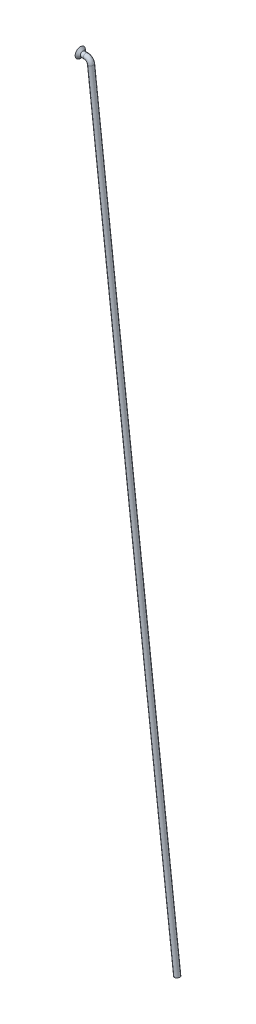
SolidWorks part; units mm, degrees
ref_plane "Plan de face" through (0, 0, 0) normal (0, 0, 1) x (1, 0, 0)
ref_plane "Plan de dessus" through (0, 0, 0) normal (0, 1, 0) x (1, 0, 0)
ref_plane "Plan de droite" through (0, 0, 0) normal (1, 0, 0) x (0, 0, -1)
sketch "Esquisse1" plane through (0, 0, 0) normal (0, 0, 1) x (1, 0, 0)
  line L1 (-1.7826, 0) -> (-4, 0)
  line L2 (0.2043, -1.7708) -> (33.8042, -293.0568)
  arc A0 (0.2043, -1.7708) -> (-1.7826, 0) centre (-1.7826, -2) ccw
  point P6 (0, 0)
  dimension "D3" = 2
  dimension "D1" = 4
  dimension "D2" = 96.58
  dimension "D4" = 295
ref_plane "Plan1" through (-4, 0, 0) normal (1, 0, 0) x (0, 0, -1)
sketch "Esquisse2" plane through (-4, 0, 0) normal (1, 0, 0) x (0, 0, -1)
  circle A0 centre (0, 0) radius 1
  dimension "D1" = 2
sweep "Balayage1" add profiles "Esquisse2" path "Esquisse1"
sketch "Esquisse3" plane through (0, 0, 0) normal (0, 0, 1) x (1, 0, 0)
  line L0 (-4, 1) -> (-4, 2)
  line L1 (-4, 2) -> (-3, 1)
  line L2 (-3, 1) -> (-4, 1)
  line L3 (-1.7826, 1) -> (-4, 1) construction
  line L4 (-4, 1) -> (-4, -1) construction
  line L5 (0, 0) -> (-9.5023, 0) construction
  line L6 (-1.7826, 0) -> (-4, 0) construction
  dimension "D1" = 4
  dimension "D2" = 1
revolve "Révolution1" add sketch "Esquisse3" angle 360 about L5
